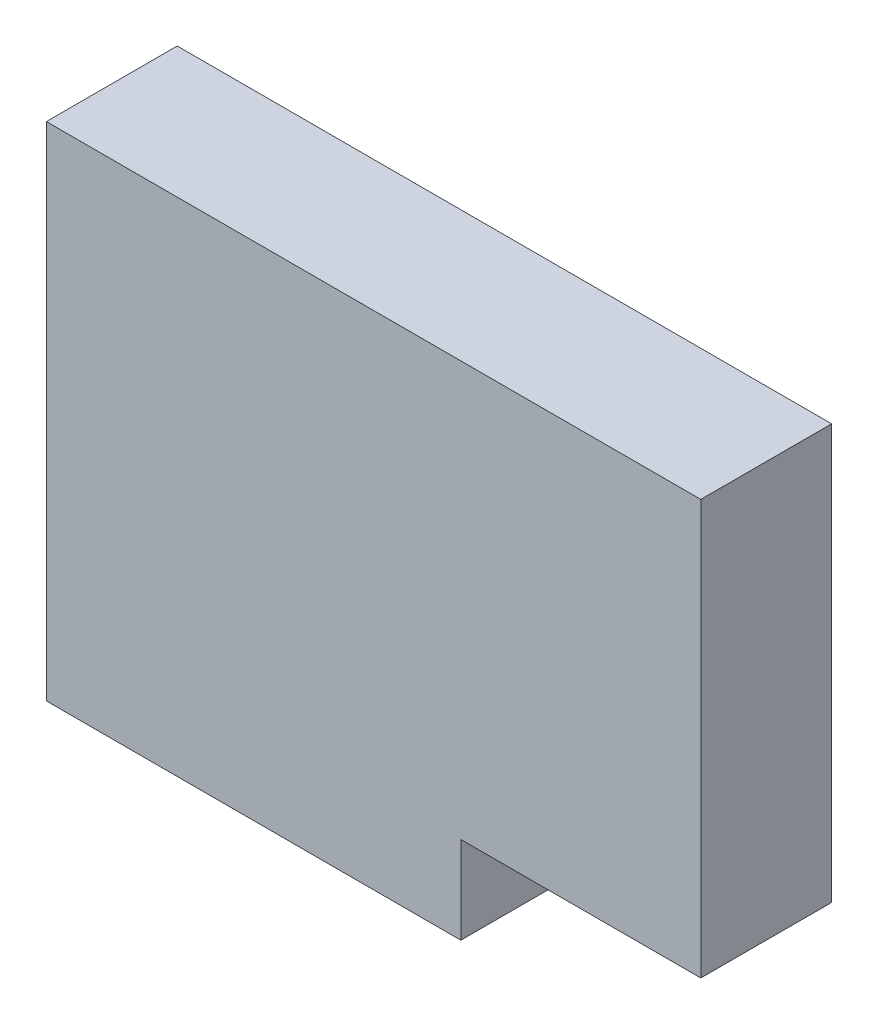
SolidWorks part; units mm, degrees
ref_plane "Front Plane" through (0, 0, 0) normal (0, 0, 1) x (1, 0, 0)
ref_plane "Top Plane" through (0, 0, 0) normal (0, 1, 0) x (1, 0, 0)
ref_plane "Right Plane" through (0, 0, 0) normal (1, 0, 0) x (0, 0, -1)
sketch "Sketch1" plane through (0, 0, 0) normal (0, 0, 1) x (1, 0, 0)
  line L1 (-381, -292.1) -> (381, -292.1)
  line L2 (-381, -292.1) -> (-381, 292.1)
  line L3 (-381, 292.1) -> (381, 292.1)
  line L4 (381, -292.1) -> (381, 292.1)
  line L5 (-381, -292.1) -> (381, 292.1) construction
  line L6 (-381, 292.1) -> (381, -292.1) construction
  point P0 (0, 0)
  dimension "D1" = 762
  dimension "D2" = 584.2
extrude "Boss-Extrude1" add sketch "Sketch1" along normal blind 152.4
sketch "Sketch2" plane through (0, 0, 152.4) normal (0, 0, 1) x (1, 0, 0)
  line L0 (381, 292.1) -> (-381, 292.1) construction
  line L1 (381, -292.1) -> (101.6, -292.1)
  line L2 (381, -292.1) -> (381, -190.5)
  line L3 (381, -190.5) -> (101.6, -190.5)
  line L4 (101.6, -292.1) -> (101.6, -190.5)
  line L5 (-381, 292.1) -> (-381, -292.1) construction
  dimension "D1" = 482.6
  dimension "D2" = 482.6
extrude "Cut-Extrude1" cut sketch "Sketch2" against normal blind 152.4
